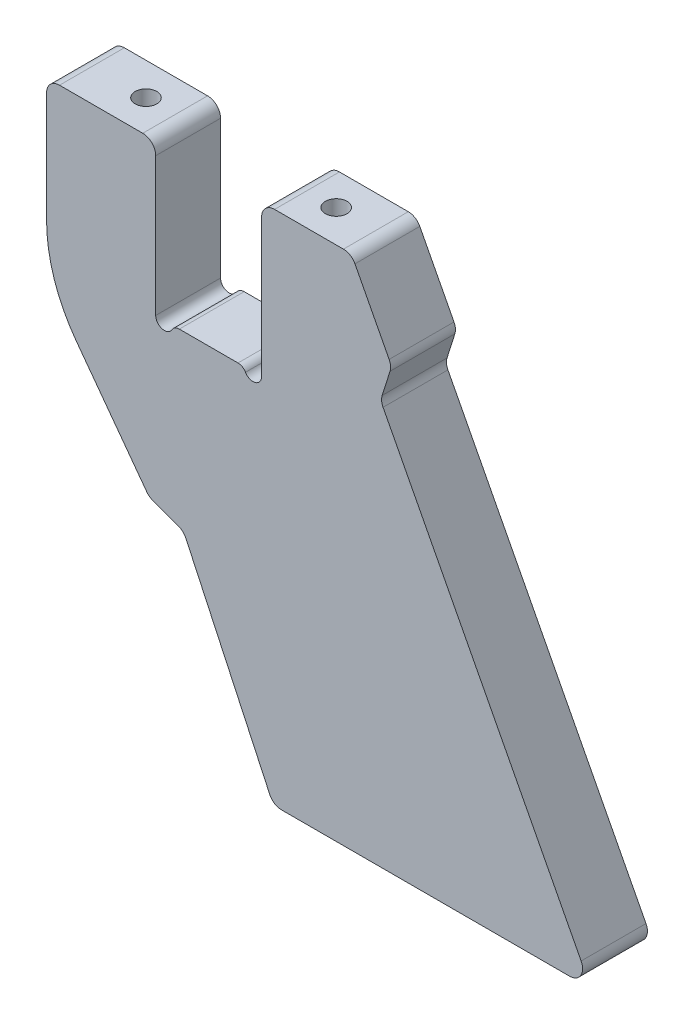
SolidWorks part; units mm, degrees
ref_plane "Plane1" through (0, 0, 0) normal (0, 0, 1) x (1, 0, 0)
ref_plane "Plane2" through (0, 0, 0) normal (0, 1, 0) x (1, 0, 0)
ref_plane "Plane3" through (0, 0, 0) normal (1, 0, 0) x (0, 0, -1)
sketch "Sketch1" plane through (0, 0, 0) normal (0, 0, 1) x (1, 0, 0)
  line L0 (-6.7859, 0) -> (6.7859, 0)
  line L1 (0, 0) -> (0, 32) construction
  line L2 (12.25, 0) -> (12.25, 32)
  line L3 (15.25, 35) -> (31.1796, 35)
  line L4 (0, 0) -> (0, 42.7803) construction
  line L5 (-30.6484, -14.2719) -> (-14.318, -36.3709)
  line L6 (40.3442, 7.8978) -> (86.1607, -80.1148)
  line L7 (-6.9749, -39.575) -> (-12.9313, -37.407)
  line L8 (83.4996, -84.5) -> (16.8547, -84.5)
  line L9 (41.7482, 18.1948) -> (33.8406, 33.3852)
  line L10 (14.1358, -82.7679) -> (-5.2821, -41.1262)
  line L11 (40.1441, 10.1851) -> (41.9484, 15.9074)
  line L23 (-37.5, 6.5288) -> (-37.5, 32)
  line L30 (-15.25, 35) -> (-34.5, 35)
  line L31 (-12.25, 0) -> (-12.25, 32)
  arc A0 (12.25, 0) -> (8.5179, -1) centre (10.25, 0) cw
  arc A1 (8.5179, -1) -> (6.7859, 0) centre (6.7859, -2) ccw
  arc A2 (-12.25, 0) -> (-8.5179, -1) centre (-10.25, 0) ccw
  arc A3 (-8.5179, -1) -> (-6.7859, 0) centre (-6.7859, -2) cw
  arc A4 (33.8406, 33.3852) -> (31.1796, 35) centre (31.1796, 32) ccw
  arc A5 (-37.5, 32) -> (-34.5, 35) centre (-34.5, 32) cw
  arc A6 (-30.6484, -14.2719) -> (-37.5, 6.5288) centre (-2.5, 6.5288) cw
  arc A7 (-15.25, 35) -> (-12.25, 32) centre (-15.25, 32) cw
  arc A8 (41.7482, 18.1948) -> (41.9484, 15.9074) centre (39.0872, 16.8095) cw
  arc A9 (-12.9313, -37.407) -> (-14.318, -36.3709) centre (-11.9053, -34.588) cw
  arc A10 (-6.9749, -39.575) -> (-5.2821, -41.1262) centre (-8.001, -42.3941) cw
  arc A11 (12.25, 32) -> (15.25, 35) centre (15.25, 32) cw
  arc A12 (16.8547, -84.5) -> (14.1358, -82.7679) centre (16.8547, -81.5) cw
  arc A13 (86.1607, -80.1148) -> (83.4996, -84.5) centre (83.4996, -81.5) cw
  arc A14 (40.3442, 7.8978) -> (40.1441, 10.1851) centre (43.0053, 9.283) cw
  point P7 (33, 35)
  point P15 (-37.5, -5)
  point P24 (39.7705, 9)
  point P27 (-13.7808, -37.0979)
  point P30 (-5.8072, -40)
  point P42 (14.9435, -84.5)
  point P45 (88.4435, -84.5)
  point P50 (39.7705, 9)
  point P53 (-12.25, 35)
  point P65 (12.25, 35)
  dimension "D3" = 26
  dimension "D13" = 35
  dimension "D23" = 2
  dimension "D5" = 3
  dimension "D11" = 33
  dimension "D18" = 3
  dimension "D19" = 3
  dimension "D21" = 3
  dimension "D4" = 27.5
  dimension "D6" = 119.5
  dimension "D7" = 24.5
  dimension "D8" = 25
  dimension "D9" = 40
  dimension "D10" = 6
  dimension "D12" = 35
  dimension "D14" = 45
  dimension "D15" = 35
  dimension "D16" = 73.5
  dimension "D17" = 45
  dimension "D20" = 6
  dimension "D22" = 37.5
extrude "Extrude1" add sketch "Sketch1" along normal blind 15
hole_wizard "Hole1" positions "Sketch3" profile "Sketch2" legacy
sketch "Sketch3" plane through (0, 35, 0) normal (0, 1, 0) x (-1, 0, 0)
  line L0 (0, 0) -> (0, 15) construction
  line L1 (-6.7859, 15) -> (6.7859, 15) construction
  line L3 (0, 7.5) -> (-22, 7.5) construction
  point P0 (-22, 7.5)
  point P12 (22, 7.5)
  dimension "D1" = 44
sketch "Sketch2" plane through (22, 35, 7.5) normal (1, 0, 0) x (0, 0, 1)
  line L0 (0, 0) -> (0, 16.5022)
  line L1 (0, 16.5022) -> (2.5, 15)
  line L2 (2.5, 15) -> (2.5, 0)
  line L4 (2.5, 0) -> (0, 0)
  line L6 (0, 16.5022) -> (-2.5, 15) construction
  line L7 (0, -4.2442) -> (0, 117.3081) construction
  dimension "Diameter" = 5
  dimension "Depth" = 15
  dimension "Drill Angle" = 118
cosmetic thread "Cosmetic Thread1" parameters "D1"=11, "D2"=6
cosmetic thread "Cosmetic Thread2" parameters "D1"=11, "D2"=6
